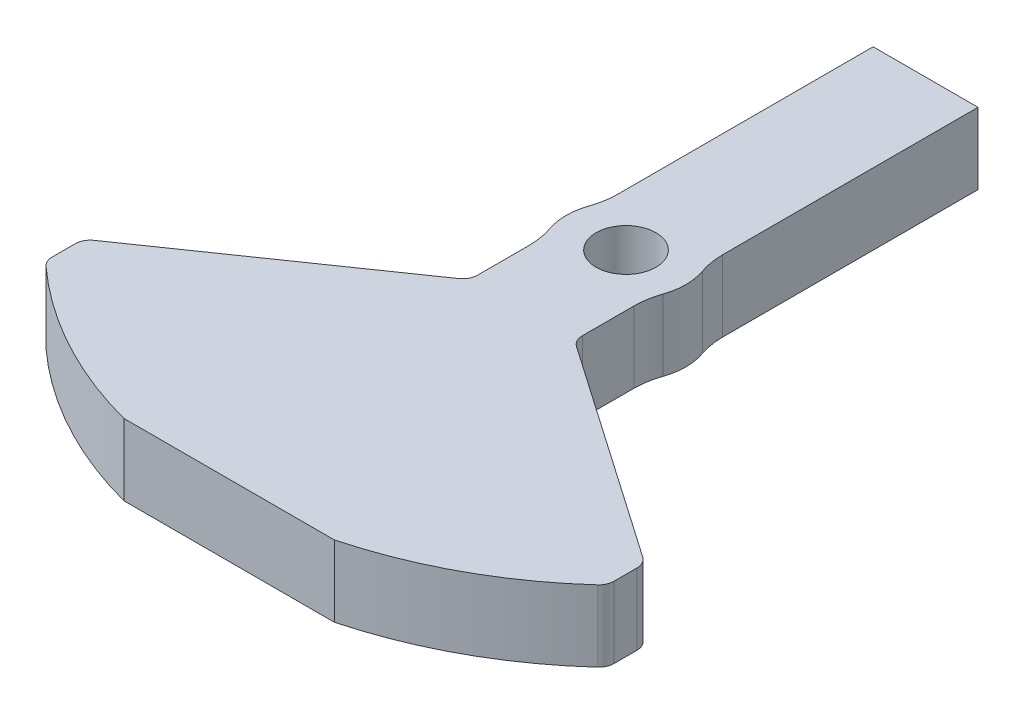
SolidWorks part; units mm, degrees
material "AISI 1020 Steel, Cold Rolled"
ref_plane "Front Plane" through (0, 0, 0) normal (0, 0, 1) x (1, 0, 0)
ref_plane "Top Plane" through (0, 0, 0) normal (0, 1, 0) x (1, 0, 0)
ref_plane "Right Plane" through (0, 0, 0) normal (1, 0, 0) x (0, 0, -1)
sketch "Sketch1" plane through (0, 0, 0) normal (0, 1, 0) x (1, 0, 0)
  line L0 (0, 0) -> (0, 70.2594) construction
  line L1 (-7, 40) -> (7, 40)
  line L2 (-7, 40) -> (-7, 3.873)
  line L3 (7, 40) -> (7, 3.873)
  line L4 (-7, -3.873) -> (-7, -13.873)
  line L5 (-14.0446, -53) -> (14.0446, -53)
  line L7 (-37.5, -35) -> (-37.5, -40)
  line L8 (-37.5, -35) -> (-7, -13.873)
  line L9 (37.5, -35) -> (37.5, -40)
  line L12 (7, -3.873) -> (7, -13.873)
  line L13 (7, -13.873) -> (37.5, -35)
  circle A0 centre (0, 0) radius 4
  arc A1 (-7, 3.873) -> (-7, -3.873) centre (0, 0) ccw
  arc A2 (7, -3.873) -> (7, 3.873) centre (0, 0) ccw
  arc A3 (-37.5, -40) -> (-14.0446, -53) centre (0, 0) ccw
  arc A4 (14.0446, -53) -> (37.5, -40) centre (0, 0) ccw
  point P15 (0, -100)
  dimension "D1" = 8
  dimension "D4" = 8
  dimension "D10" = 53
  dimension "D2" = 14
  dimension "D3" = 7
  dimension "D5" = 40
  dimension "D6" = 40
  dimension "D7" = 75
  dimension "D8" = 10
  dimension "D9" = 5
extrude "Boss-Extrude1" add sketch "Sketch1" along normal blind 9.525
fillet "Fillet1" radius 10 4 edges at (-7, 4.7625, -3.873) (7, 4.7625, -3.873) (7, 4.7625, 3.873) (-7, 4.7625, 3.873)
hole_wizard "M8x1.25 Tapped Hole1" positions "Sketch3" profile "Sketch2" tap size "M8x1.25" standard "ANSI Metric"
sketch "Sketch3" plane through (0, 0, -40) normal (0, 0, -1) x (-1, 0, 0)
  line L0 (-7, 4.7625) -> (7, 4.7625) construction
  line L1 (-7, 9.525) -> (-7, 0) construction
  line L2 (7, 9.525) -> (7, 0) construction
  point P0 (0, 4.7625)
  dimension "D1" = 0
sketch "Sketch2" plane through (0, 4.7625, -40) normal (1, 0, 0) x (0, 1, 0)
  line L0 (0, 0) -> (0, 34.2929)
  line L1 (0, 34.2929) -> (3.4, 32.25)
  line L2 (3.4, 32.25) -> (3.4, 0)
  line L5 (3.4, 0) -> (0, 0)
  line L10 (0, 34.2929) -> (-3.4, 32.25) construction
  line L11 (0, -6.35) -> (0, 107.95) construction
  dimension "Tap Drill Dia." = 6.8
  dimension "Tap Drill Depth" = 32.25
  dimension "Drill Angle" = 118
fillet "Fillet2" radius 2 6 edges at (37.5, 4.7625, 35) (7, 4.7625, 13.873) (-7, 4.7625, 13.873) (-37.5, 4.7625, 40) (-37.5, 4.7625, 35) (37.5, 4.7625, 40)
